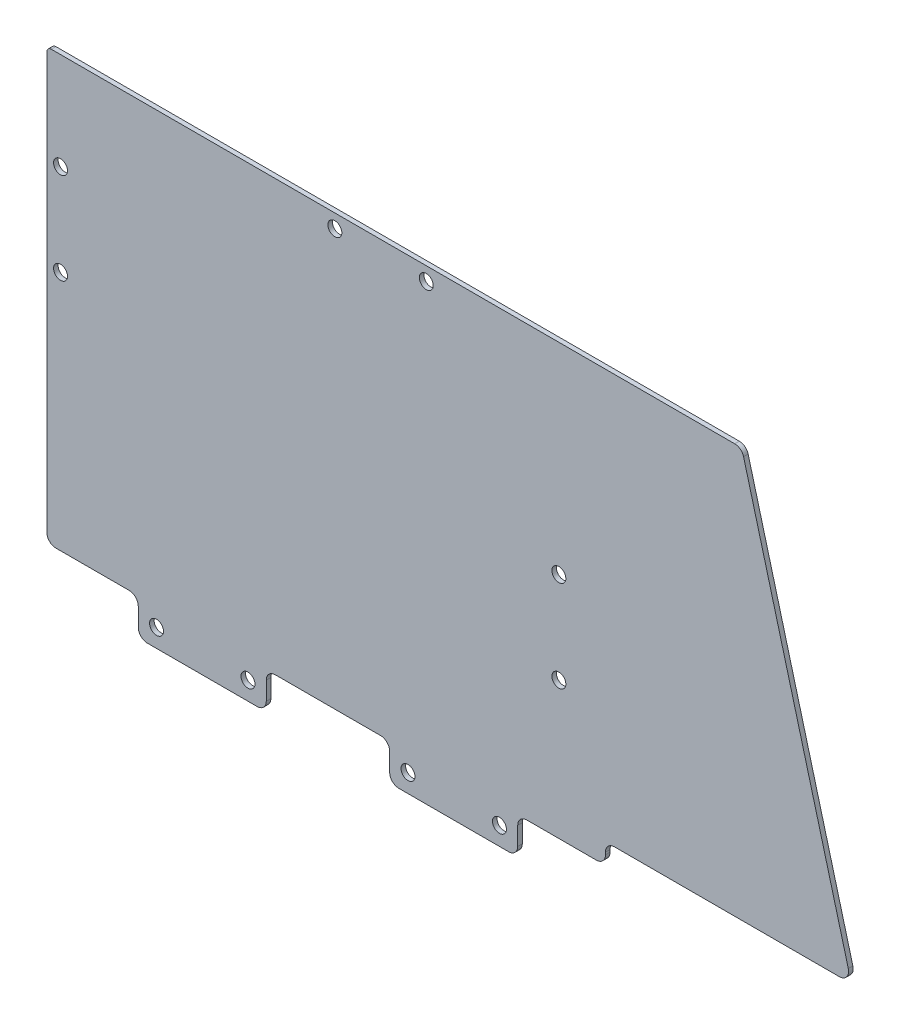
SolidWorks part; units mm, degrees
material "Thornel Mat VMA"
ref_plane "前视基准面" through (0, 0, 0) normal (0, 0, 1) x (1, 0, 0)
ref_plane "上视基准面" through (0, 0, 0) normal (0, 1, 0) x (1, 0, 0)
ref_plane "右视基准面" through (0, 0, 0) normal (1, 0, 0) x (0, 0, -1)
other "Configuration Table"
sketch "草图1" plane through (0, 0, 0) normal (0, 0, 1) x (1, 0, 0)
  line L0 (0, 0) -> (20, 0) construction
  line L2 (24, 4) -> (-4, 4)
  line L3 (24, 4) -> (24, -4)
  line L4 (24, -4) -> (-4, -4)
  line L5 (-4, 4) -> (-4, -4)
  line L6 (24, 4) -> (-4, -4) construction
  line L7 (24, -4) -> (-4, 4) construction
  line L8 (-51, 120) -> (67, 120)
  line L9 (-51, 120) -> (-51, 4)
  line L10 (-51, 4) -> (67, 4)
  line L11 (67, 120) -> (67, 4)
  circle A0 centre (0, 0) radius 1.525
  circle A1 centre (20, 0) radius 1.525
  point P5 (10, 0)
  dimension "D2" = 3.05
  dimension "D3" = 4
  dimension "D4" = 4
  dimension "D5" = 51
  dimension "D6" = 67
  dimension "D7" = 120
  dimension "D1" = 20
extrude "凸台-拉伸1" add sketch "草图1" along normal blind 1 contours L11 L8 L9 L10 L2 | L2 L5 L4 L3 A1 A0
fillet "圆角1" radius 2 8 edges at (67, 4, 0.5) (24, 4, 0.5) (24, -4, 0.5) (-4, -4, 0.5) (-4, 4, 0.5) (-51, 4, 0.5) (-51, 120, 0.5) (67, 120, 0.5)
sketch "草图3" plane through (0, 0, 1) normal (0, 0, 1) x (1, 0, 0)
  line L0 (-48, 76.75) -> (-48, 56.75) construction
  line L1 (-49, 120) -> (65, 120) construction
  line L2 (-51, 118) -> (-51, 6) construction
  circle A0 centre (-48, 76.75) radius 1.525
  circle A1 centre (-48, 56.75) radius 1.525
  dimension "D1" = 43.25
  dimension "D2" = 20
  dimension "D4" = 3.05
  dimension "D3" = 3
extrude "切除-拉伸1" cut sketch "草图3" against normal blind 10
sketch "草图4" plane through (0, 0, 1) normal (0, 0, 1) x (1, 0, 0)
  line L0 (67, 4) -> (67, 85) construction
  line L1 (26, 4) -> (65, 4) construction
  line L2 (67, 118) -> (67, 6) construction
  line L3 (-24, 120) -> (-24, 98)
  line L4 (-24, 98) -> (67, 98)
  line L5 (-51, 118) -> (-51, 120) construction
  line L6 (-51, 120) -> (-49, 120) construction
  line L7 (-49, 120) -> (65, 120) construction
  line L15 (26, 4) -> (65, 4)
  line L16 (67, 6) -> (67, 118)
  line L17 (65, 120) -> (-49, 120)
  line L18 (-51, 118) -> (-51, 6)
  line L19 (-49, 4) -> (-6, 4)
  line L20 (-4, 2) -> (-4, -2)
  line L21 (-2, -4) -> (22, -4)
  line L22 (24, -2) -> (24, 2)
  line L23 (26, 4) -> (65, 4)
  line L24 (67, 6) -> (67, 118)
  line L25 (65, 120) -> (-49, 120)
  line L26 (-51, 118) -> (-51, 6)
  line L27 (-49, 4) -> (-6, 4)
  line L28 (-4, 2) -> (-4, -2)
  line L29 (-2, -4) -> (22, -4)
  line L30 (24, -2) -> (24, 2)
  arc A8 (65, 4) -> (67, 6) centre (65, 6) ccw
  arc A9 (67, 118) -> (65, 120) centre (65, 118) ccw
  arc A10 (-49, 120) -> (-51, 118) centre (-49, 118) ccw
  arc A11 (-51, 6) -> (-49, 4) centre (-49, 6) ccw
  arc A12 (-4, 2) -> (-6, 4) centre (-6, 2) ccw
  arc A13 (-4, -2) -> (-2, -4) centre (-2, -2) ccw
  arc A14 (22, -4) -> (24, -2) centre (22, -2) ccw
  arc A15 (26, 4) -> (24, 2) centre (26, 2) ccw
  arc A16 (65, 4) -> (67, 6) centre (65, 6) ccw
  arc A17 (67, 118) -> (65, 120) centre (65, 118) ccw
  arc A18 (-49, 120) -> (-51, 118) centre (-49, 118) ccw
  arc A19 (-51, 6) -> (-49, 4) centre (-49, 6) ccw
  arc A20 (-4, 2) -> (-6, 4) centre (-6, 2) ccw
  arc A21 (-4, -2) -> (-2, -4) centre (-2, -2) ccw
  arc A22 (22, -4) -> (24, -2) centre (22, -2) ccw
  arc A23 (26, 4) -> (24, 2) centre (26, 2) ccw
  dimension "D1" = 81
  dimension "D4" = 25
  dimension "D5" = 94
  dimension "D2" = 0
extrude "切除-拉伸2" cut sketch "草图4" against normal blind 10
sketch "草图5" plane through (0, 0, 1) normal (0, 0, 1) x (1, 0, 0)
  line L0 (61, 4) -> (61, 34) construction
  line L1 (26, 4) -> (65, 4) construction
  line L2 (61, 54) -> (61, 34) construction
  line L3 (67, 98) -> (67, 6) construction
  circle A0 centre (61, 34) radius 1.525
  circle A1 centre (61, 54) radius 1.525
  dimension "D2" = 3.05
  dimension "D1" = 20
  dimension "D3" = 30
  dimension "D4" = 6
extrude "切除-拉伸3" cut sketch "草图5" against normal blind 10
fillet "圆角3" radius 2 3 edges at (-24, 98, 0.5) (-24, 120, 0.5) (67, 98, 0.5)
sketch "草图8" plane through (0, 0, 1) normal (0, 0, 1) x (1, 0, 0)
  line L0 (12, 95) -> (32, 95) construction
  line L1 (-22, 98) -> (65, 98) construction
  line L2 (67, 96) -> (67, 6) construction
  circle A0 centre (12, 95) radius 1.525
  circle A1 centre (32, 95) radius 1.525
  dimension "D2" = 3.05
  dimension "D4" = 35
  dimension "D1" = 3
  dimension "D3" = 20
extrude "切除-拉伸5" cut sketch "草图8" against normal mid plane 10
sketch "草图9" plane through (0, 0, 1) normal (0, 0, 1) x (1, 0, 0)
  line L0 (-51, 118) -> (-51, 6) construction
  line L1 (-22, 98) -> (-51, 98)
  line L2 (-22, 98) -> (-22, 120)
  line L3 (-22, 120) -> (-51, 120)
  line L4 (-51, 98) -> (-51, 120)
  line L5 (-49, 120) -> (-26, 120) construction
extrude "切除-拉伸6" cut sketch "草图9" against normal mid plane 22
fillet "圆角4" radius 1 1 edges at (-51, 98, 0.5)
sketch "草图11" plane through (0, 0, 0) normal (0, 0, -1) x (-1, 0, 0)
  line L0 (-65, 98) -> (-101, 98)
  line L1 (-101, 98) -> (-126.1872, 4)
  line L2 (-126.1872, 4) -> (-63.0245, 4)
  line L3 (-26, 4) -> (-65, 4) construction
  line L4 (-101, 98) -> (-101, 4) construction
  line L12 (51, 6) -> (51, 97)
  line L13 (50, 98) -> (-65, 98)
  line L14 (-67, 96) -> (-67, 6)
  line L15 (-65, 4) -> (-26, 4)
  line L16 (-24, 2) -> (-24, -2)
  line L17 (-22, -4) -> (2, -4)
  line L18 (4, -2) -> (4, 2)
  line L19 (6, 4) -> (49, 4)
  line L20 (51, 6) -> (51, 97)
  line L21 (50, 98) -> (-65, 98)
  line L22 (-67, 96) -> (-67, 6)
  line L23 (-65, 4) -> (-26, 4)
  line L24 (-24, 2) -> (-24, -2)
  line L25 (-22, -4) -> (2, -4)
  line L26 (4, -2) -> (4, 2)
  line L27 (6, 4) -> (49, 4)
  arc A8 (51, 97) -> (50, 98) centre (50, 97) ccw
  arc A9 (-65, 98) -> (-67, 96) centre (-65, 96) ccw
  arc A10 (-67, 6) -> (-65, 4) centre (-65, 6) ccw
  arc A11 (-24, 2) -> (-26, 4) centre (-26, 2) ccw
  arc A12 (-24, -2) -> (-22, -4) centre (-22, -2) ccw
  arc A13 (2, -4) -> (4, -2) centre (2, -2) ccw
  arc A14 (6, 4) -> (4, 2) centre (6, 2) ccw
  arc A15 (49, 4) -> (51, 6) centre (49, 6) ccw
  arc A17 (-65, 98) -> (-67, 96) centre (-65, 96) ccw
  arc A18 (-67, 6) -> (-65, 4) centre (-65, 6) ccw
  arc A19 (-24, 2) -> (-26, 4) centre (-26, 2) ccw
  arc A20 (-24, -2) -> (-22, -4) centre (-22, -2) ccw
  arc A21 (2, -4) -> (4, -2) centre (2, -2) ccw
  arc A22 (6, 4) -> (4, 2) centre (6, 2) ccw
  arc A23 (49, 4) -> (51, 6) centre (49, 6) ccw
  arc A24 (51, 97) -> (50, 98) centre (50, 97) ccw
  arc M27 (-65, 98) -> (-67, 96) centre (-65, 96) ccw
  line M28 (-67, 96) -> (-67, 6)
  arc M29 (-67, 6) -> (-65, 4) centre (-65, 6) ccw
  dimension "D2" = 36
  dimension "D3" = 15
  dimension "D1" = 0
extrude "凸台-拉伸2" add sketch "草图11" against normal up to surface (1 mm away) contours L0 L4 L2 M29 M28 M27 | L4 L1 L2
sketch "草图12" plane through (0, 0, 1) normal (0, 0, 1) x (1, 0, 0)
  line L1 (126.1872, 4) -> (71.1872, 4)
  line L2 (126.1872, 4) -> (126.1872, 8.5)
  line L3 (126.1872, 8.5) -> (71.1872, 8.5)
  line L4 (71.1872, 4) -> (71.1872, 8.5)
  dimension "D1" = 4.5
  dimension "D2" = 55
extrude "切除-拉伸7" cut sketch "草图12" against normal blind 10
fillet "圆角5" radius 2 4 edges at (101, 98, 0.5) (71.1872, 4, 0.5) (71.1872, 8.5, 0.5) (124.9815, 8.5, 0.5)
sketch "草图13" plane through (0, 0, 1) normal (0, 0, 1) x (1, 0, 0)
  line L0 (22, -4) -> (-2, -4) construction
  line L1 (-6, 4) -> (26, 4)
  line L2 (-6, 4) -> (-6, -4)
  line L3 (-6, -4) -> (26, -4)
  line L4 (26, 4) -> (26, -4)
  arc A0 (-4, 2) -> (-6, 4) centre (-6, 2) ccw construction
  point P9 (26, 4)
extrude "切除-拉伸8" cut sketch "草图13" against normal blind 10
sketch "草图14" plane through (0, 0, 1) normal (0, 0, 1) x (1, 0, 0)
  line L0 (-27, 0) -> (-7, 0) construction
  line L1 (-7, 0) -> (28, 0) construction
  line L2 (28, 0) -> (48, 0) construction
  line L3 (-51, 97) -> (-51, 6) construction
  line L4 (-49, 4) -> (69.1872, 4) construction
  line L6 (-3, -4) -> (-31, -4)
  line L7 (-3, -4) -> (-3, 4)
  line L8 (-3, 4) -> (-31, 4)
  line L9 (-31, -4) -> (-31, 4)
  line L10 (-3, -4) -> (-31, 4) construction
  line L11 (-3, 4) -> (-31, -4) construction
  line L12 (52, -4) -> (24, -4)
  line L13 (52, -4) -> (52, 4)
  line L14 (52, 4) -> (24, 4)
  line L15 (24, -4) -> (24, 4)
  line L16 (52, -4) -> (24, 4) construction
  line L17 (52, 4) -> (24, -4) construction
  circle A0 centre (-27, 0) radius 1.525
  circle A1 centre (-7, 0) radius 1.525
  circle A2 centre (28, 0) radius 1.525
  circle A3 centre (48, 0) radius 1.525
  point P10 (38, 0)
  point P14 (-17, 0)
  dimension "D1" = 3.05
  dimension "D2" = 24
  dimension "D4" = 55
  dimension "D6" = 4
  dimension "D3" = 20
  dimension "D5" = 4
extrude "凸台-拉伸3" add sketch "草图14" against normal up to surface (1 mm away) up to face at (44.2954, 36.9733, 0)
fillet "圆角6" radius 2 8 edges at (52, -4, 0.5) (52, 4, 0.5) (24, 4, 0.5) (24, -4, 0.5) (-3, -4, 0.5) (-3, 4, 0.5) (-31, 4, 0.5) (-31, -4, 0.5)
